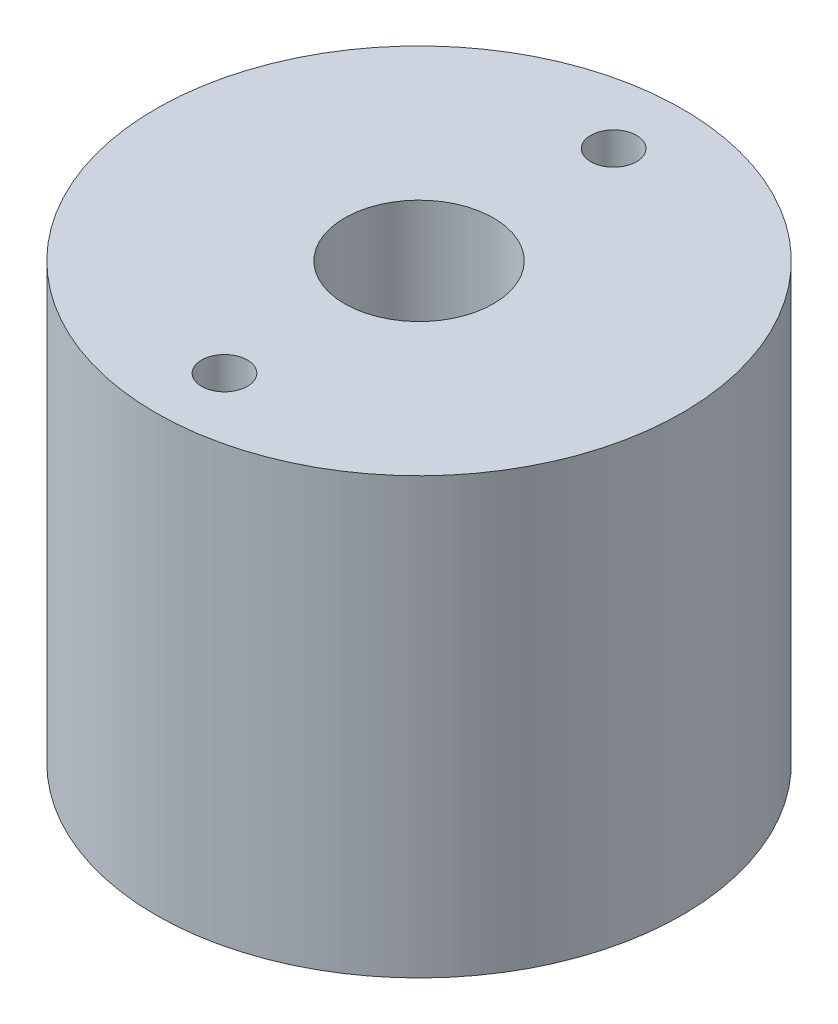
SolidWorks part; units mm, degrees
ref_plane "Front Plane" through (0, 0, 0) normal (0, 0, 1) x (1, 0, 0)
ref_plane "Top Plane" through (0, 0, 0) normal (0, 1, 0) x (1, 0, 0)
ref_plane "Right Plane" through (0, 0, 0) normal (1, 0, 0) x (0, 0, -1)
sketch "Sketch1" plane through (0, 0, 0) normal (0, 1, 0) x (1, 0, 0)
  circle A0 centre (0, 0) radius 11.5
  dimension "D1" = 23
extrude "Boss-Extrude1" add sketch "Sketch1" along normal blind 19
sketch "Sketch2" plane through (0, 19, 0) normal (0, 1, 0) x (1, 0, 0)
  line L0 (0, 8.5) -> (0, -8.5) construction
  circle A0 centre (0, 0) radius 8.5 construction
  circle A1 centre (0, 8.5) radius 1
  circle A2 centre (0, -8.5) radius 1
  circle A3 centre (0, 0) radius 3.25
  dimension "D1" = 17
  dimension "D2" = 2
  dimension "D3" = 6.5
extrude "Cut-Extrude1" cut sketch "Sketch2" against normal blind 8.5
